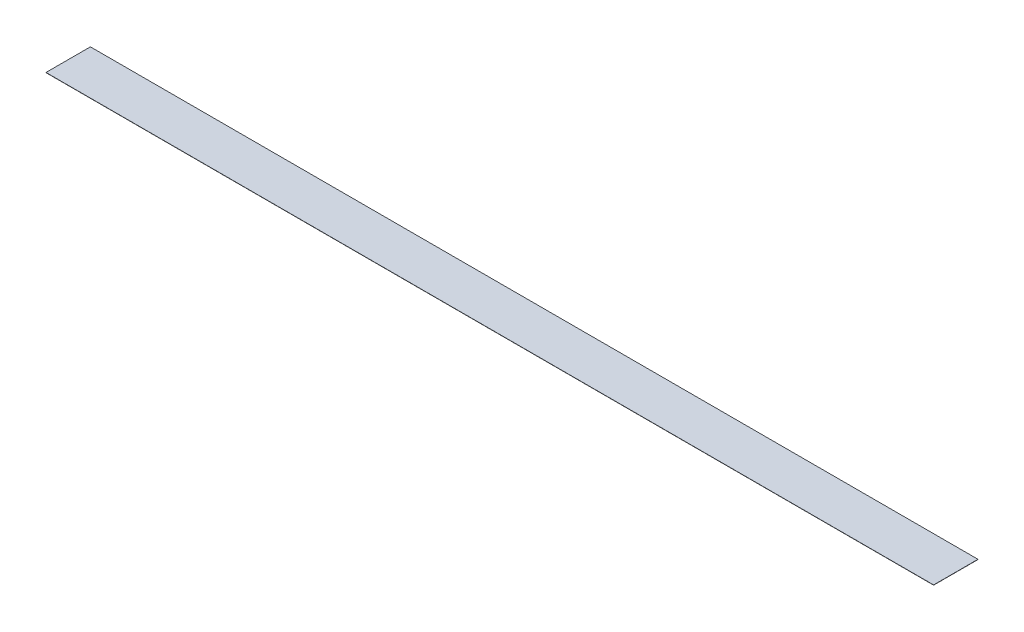
SolidWorks part; units mm, degrees
ref_plane "Front Plane" through (0, 0, 0) normal (0, 0, 1) x (1, 0, 0)
ref_plane "Top Plane" through (0, 0, 0) normal (0, 1, 0) x (1, 0, 0)
ref_plane "Right Plane" through (0, 0, 0) normal (1, 0, 0) x (0, 0, -1)
sketch "Sketch1" plane through (0, 0, 0) normal (0, 1, 0) x (1, 0, 0)
  line L1 (-508, 25.4) -> (508, 25.4)
  line L2 (-508, 25.4) -> (-508, -25.4)
  line L3 (-508, -25.4) -> (508, -25.4)
  line L4 (508, 25.4) -> (508, -25.4)
  line L5 (-508, 25.4) -> (508, -25.4) construction
  line L6 (-508, -25.4) -> (508, 25.4) construction
  point P0 (0, 0)
  dimension "D1" = 50.8
  dimension "D2" = 1016
extrude "Boss-Extrude1" add sketch "Sketch1" along normal blind 0.254
